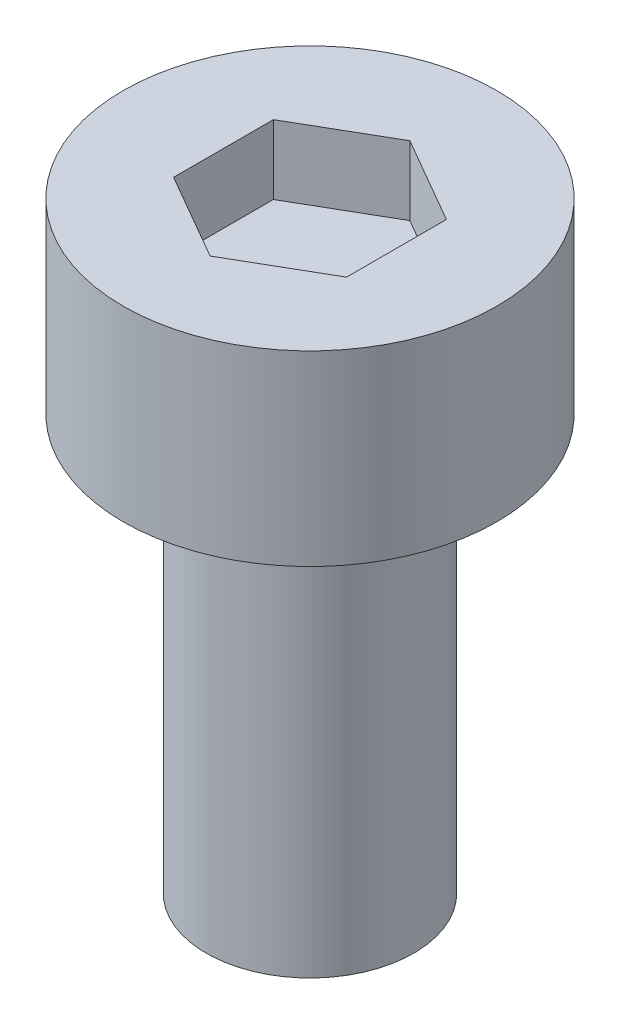
SolidWorks part; units mm, degrees
ref_plane "Front Plane" through (0, 0, 0) normal (0, 0, 1) x (1, 0, 0)
ref_plane "Top Plane" through (0, 0, 0) normal (0, 1, 0) x (1, 0, 0)
ref_plane "Right Plane" through (0, 0, 0) normal (1, 0, 0) x (0, 0, -1)
sketch "Sketch1" plane through (0, 0, 0) normal (0, 1, 0) x (1, 0, 0)
  circle A0 centre (0, 0) radius 2.7
extrude "Boss-Extrude1" add sketch "Sketch1" along normal blind 2.7
sketch "Sketch2" plane through (0, 2.7, 0) normal (0, 1, 0) x (1, 0, 0)
  line L1 (0, 1.4434) -> (-1.25, 0.7217)
  line L2 (-1.25, 0.7217) -> (-1.25, -0.7217)
  line L3 (-1.25, -0.7217) -> (0, -1.4434)
  line L4 (0, -1.4434) -> (1.25, -0.7217)
  line L5 (1.25, -0.7217) -> (1.25, 0.7217)
  line L6 (1.25, 0.7217) -> (0, 1.4434)
  circle A0 centre (0, 0) radius 1.25 construction
extrude "Cut-Extrude1" cut sketch "Sketch2" against normal blind 1
sketch "Sketch3" plane through (0, 0, 0) normal (0, -1, 0) x (1, 0, 0)
  circle A0 centre (0, 0) radius 1.5
extrude "Boss-Extrude2" add sketch "Sketch3" along normal blind 6
